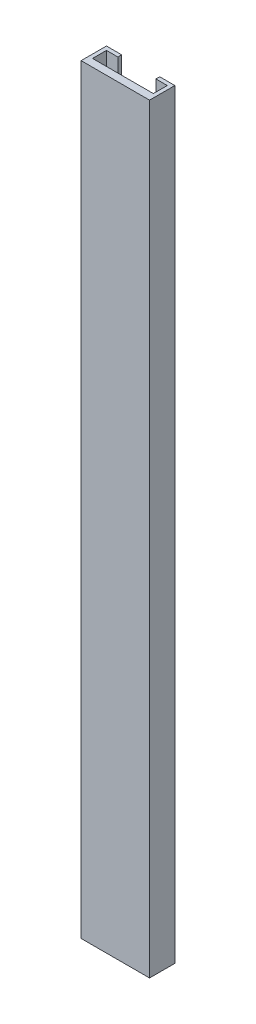
SolidWorks part; units mm, degrees
ref_plane "Plan de face" through (0, 0, 0) normal (0, 0, 1) x (1, 0, 0)
ref_plane "Plan de dessus" through (0, 0, 0) normal (0, 1, 0) x (1, 0, 0)
ref_plane "Plan de droite" through (0, 0, 0) normal (1, 0, 0) x (0, 0, -1)
sketch "Esquisse1" plane through (0, 0, 0) normal (0, 1, 0) x (1, 0, 0)
  line L0 (-13.5, 0) -> (13.5, 0)
  line L5 (13.5, 0) -> (13.5, 10)
  line L6 (13.5, 10) -> (7.5, 10)
  line L7 (7.5, 10) -> (7.5, 8.5)
  line L8 (7.5, 8.5) -> (12, 8.5)
  line L9 (12, 8.5) -> (12, 3)
  line L10 (12, 3) -> (-12, 3)
  line L11 (0, 8.85) -> (0, -6.25) construction
  line L12 (-7.5, 10) -> (-7.5, 8.5)
  line L13 (-7.5, 8.5) -> (-12, 8.5)
  line L14 (-13.5, 10) -> (-7.5, 10)
  line L15 (-13.5, 0) -> (-13.5, 10)
  line L16 (-12, 8.5) -> (-12, 3)
  point P9 (0, 0)
  point P17 (0, 3)
  dimension "D1" = 3
  dimension "D2" = 1.5
  dimension "D3" = 1.5
  dimension "D4" = 13.5
  dimension "D5" = 10
  dimension "D6" = 6
extrude "Boss.-Extru.1" add sketch "Esquisse1" along normal blind 300
